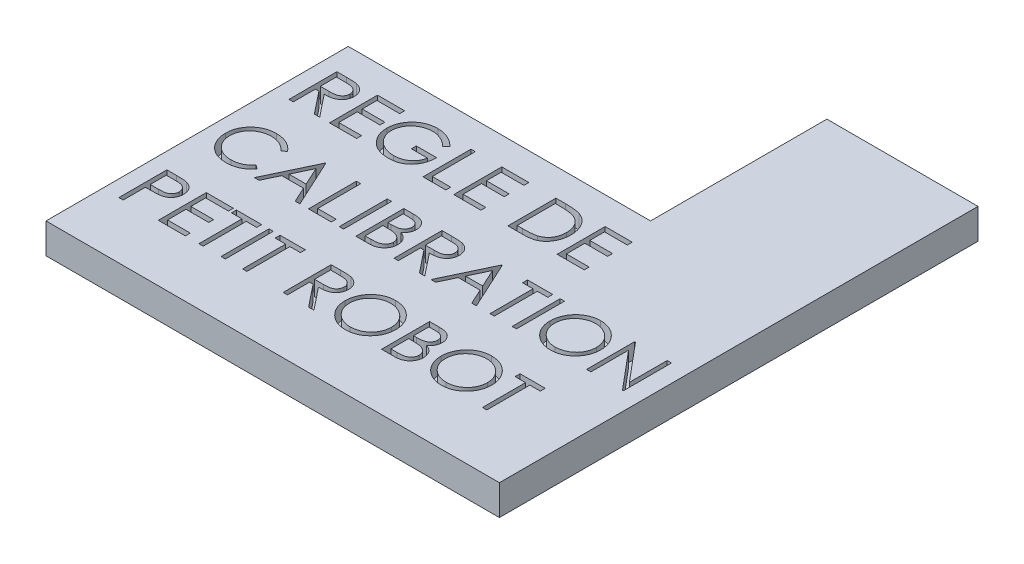
SolidWorks part; units mm, degrees
ref_plane "Plan de face" through (0, 0, 0) normal (0, 0, 1) x (1, 0, 0)
ref_plane "Plan de dessus" through (0, 0, 0) normal (0, 1, 0) x (1, 0, 0)
ref_plane "Plan de droite" through (0, 0, 0) normal (1, 0, 0) x (0, 0, -1)
sketch "Esquisse1" plane through (0, 0, 0) normal (0, 1, 0) x (1, 0, 0)
  line L1 (0, 52.33) -> (60, 52.33)
  line L2 (0, 52.33) -> (0, -7.67)
  line L3 (0, -7.67) -> (60, -7.67)
  line L6 (60, 52.33) -> (60, 87.33)
  line L7 (60, 87.33) -> (90, 87.33)
  line L8 (90, 52.33) -> (90, 87.33)
  line L10 (90, 52.33) -> (90, -7.67)
  line L11 (90, -7.67) -> (60, -7.67)
extrude "Boss.-Extru.1" add sketch "Esquisse1" along normal blind 6
sketch "texte" plane through (0, 6, 0) normal (0, 1, 0) x (1, 0, 0)
  line L0 (60, 52.33) -> (0, 52.33) construction
  line L1 (0, 52.33) -> (0, -7.67) construction
  text T0 "REGLE DE\r\nCALIBRATION \r\nPETIT ROBOT" font "Century Gothic" height in points 36
  dimension "D1" = 15
  dimension "D2" = 2
extrude "Enlèv. mat.-Extru.2" cut sketch "texte" against normal blind 3
